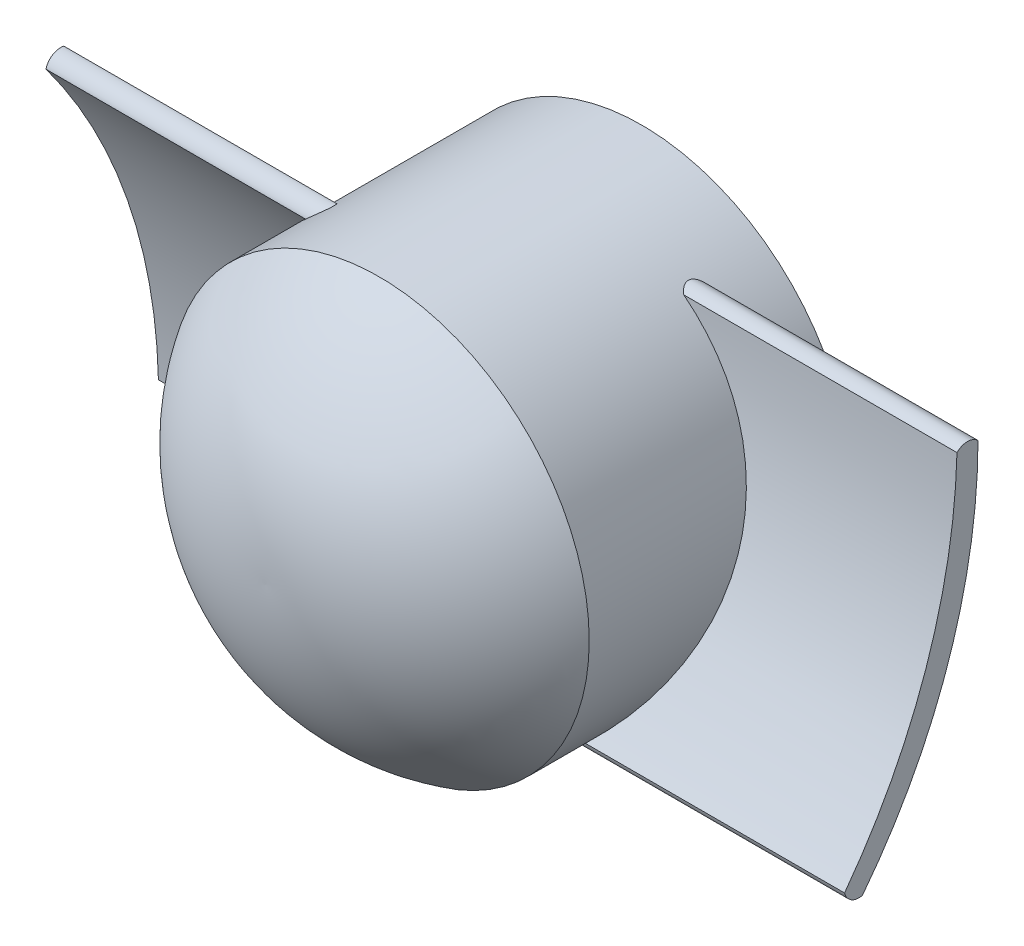
SolidWorks part; units mm, degrees
material "Air"
ref_plane "Front Plane" through (0, 0, 0) normal (0, 0, 1) x (1, 0, 0)
ref_plane "Top Plane" through (0, 0, 0) normal (0, 1, 0) x (1, 0, 0)
ref_plane "Right Plane" through (0, 0, 0) normal (1, 0, 0) x (0, 0, -1)
sketch "Sketch1" plane through (0, 0, 0) normal (0, 0, 1) x (1, 0, 0)
  circle A0 centre (0, 0) radius 20
extrude "Extrude1" add sketch "Sketch1" along normal blind 25
sketch "Sketch2" plane through (0, 0, 0) normal (1, 0, 0) x (0, 0, -1)
  line L0 (-25, 0) -> (-35.8075, 0)
  line L1 (-25, 20) -> (-25, -20) construction
  line L2 (-25, 0) -> (-25, 20)
  arc A0 (-25, 20) -> (-35.8075, 0) centre (-13.0657, 0.631) ccw
revolve "Revolve1" add sketch "Sketch2" angle 360 about L0
sketch "Sketch3" plane through (0, 0, 0) normal (1, 0, 0) x (0, 0, -1)
  line L2 (0, -20) -> (0, 20) construction
  line L3 (0, 20) -> (-25, 20) construction
  line L4 (-25, -20) -> (0, -20) construction
  arc A0 (-17, -16) -> (-6, 16) centre (-58.266, 16.0758) ccw
  arc A1 (-18.7, -14.9464) -> (-8, 16) centre (-61.9565, 17.3329) ccw
  arc A2 (-18.7, -14.9464) -> (-17, -16) centre (-17.3232, -14.6232) ccw
  arc A3 (-8, 16) -> (-6, 16) centre (-7, 15) cw
  point P0 (-8, 16)
  point P1 (-6, 16)
  point P2 (-17, -16)
  point P3 (-18.7, -14.9464)
  dimension "D1" = 2
  dimension "D2" = 2
  dimension "D3" = 6
  dimension "D4" = 4
  dimension "D5" = 4
  dimension "D6" = 4
  dimension "D7" = 17
  dimension "D8" = 18.7
extrude "Extrude2" add sketch "Sketch3" along normal blind 38
sketch "Sketch4" plane through (0, 0, 0) normal (1, 0, 0) x (0, 0, -1)
  line L0 (0, -20) -> (0, 20) construction
  line L3 (0, 0) -> (-25, 0) construction
  line L4 (-25, 20) -> (-25, -20) construction
  arc A4 (-8, -16) -> (-6, -16) centre (-7, -14.5538) ccw
  arc A5 (-18.7, 14.9464) -> (-17, 16) centre (-17.3232, 14.6232) cw
  arc A6 (-18.7, 14.9464) -> (-8, -16) centre (-61.9565, -17.3329) cw
  arc A7 (-17, 16) -> (-6, -16) centre (-58.266, -16.0758) cw
extrude "Extrude3" add sketch "Sketch4" against normal blind 38
